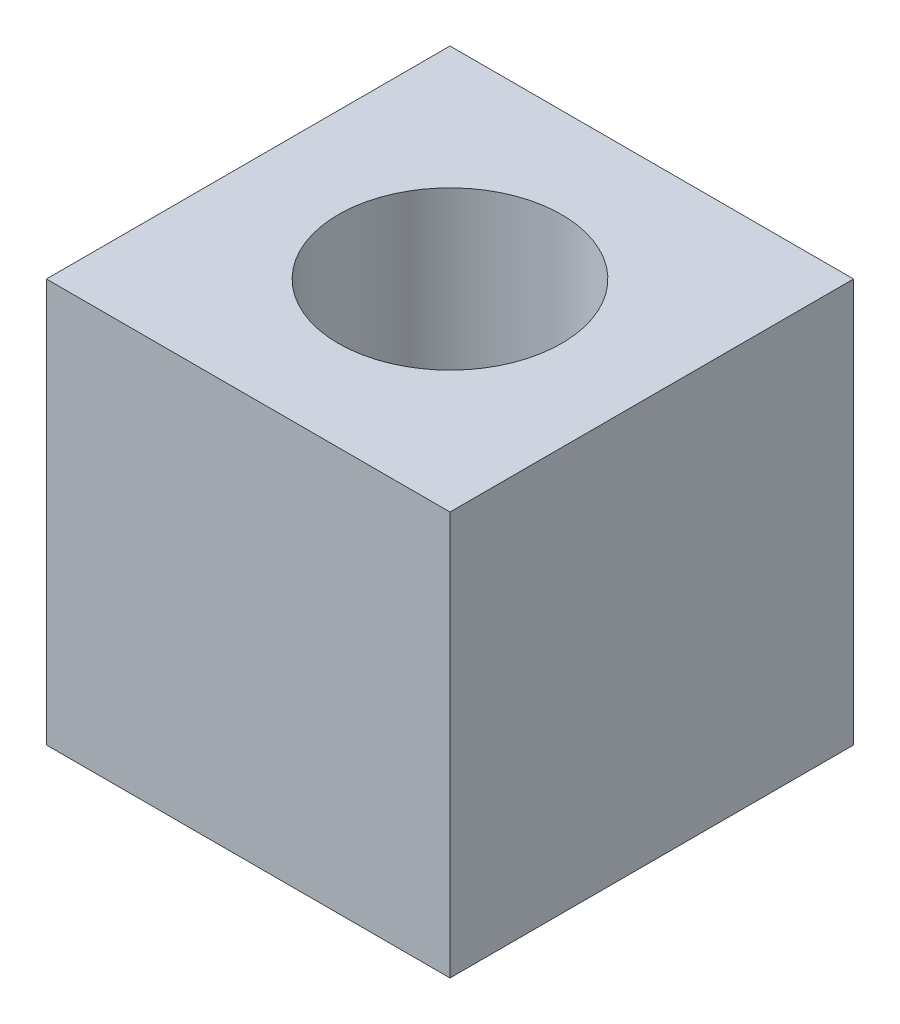
SolidWorks part; units mm, degrees
ref_plane "Plan de face" through (0, 0, 0) normal (0, 0, 1) x (1, 0, 0)
ref_plane "Plan de dessus" through (0, 0, 0) normal (0, 1, 0) x (1, 0, 0)
ref_plane "Plan de droite" through (0, 0, 0) normal (1, 0, 0) x (0, 0, -1)
sketch "Esquisse1" plane through (0, 0, 0) normal (0, 1, 0) x (1, 0, 0)
  line L0 (-7.5, 7.5) -> (7.5, 7.5)
  line L1 (-7.5, 7.5) -> (-7.5, -7.5)
  line L2 (7.5, 7.5) -> (7.5, -7.5)
  line L3 (-7.5, -7.5) -> (7.5, -7.5)
  line L4 (0, 0) -> (0, -7.5) construction
  line L5 (7.5, 0) -> (0, 0) construction
  circle A0 centre (0, 0) radius 4.15
  dimension "D3" = 8.3
  dimension "D1" = 15
  dimension "D2" = 15
extrude "Boss.-Extru.1" add sketch "Esquisse1" along normal blind 15
sketch "Esquisse2" plane through (0, 0, 0) normal (0, 0, 1) x (1, 0, 0)
  line L0 (0, 0) -> (0, 7.5) construction
  circle A0 centre (0, 7.5) radius 2.15
  dimension "D2" = 4.3
  dimension "D1" = 7.5
extrude "Enlèv. mat.-Extru.1" cut sketch "Esquisse2" against normal through all
